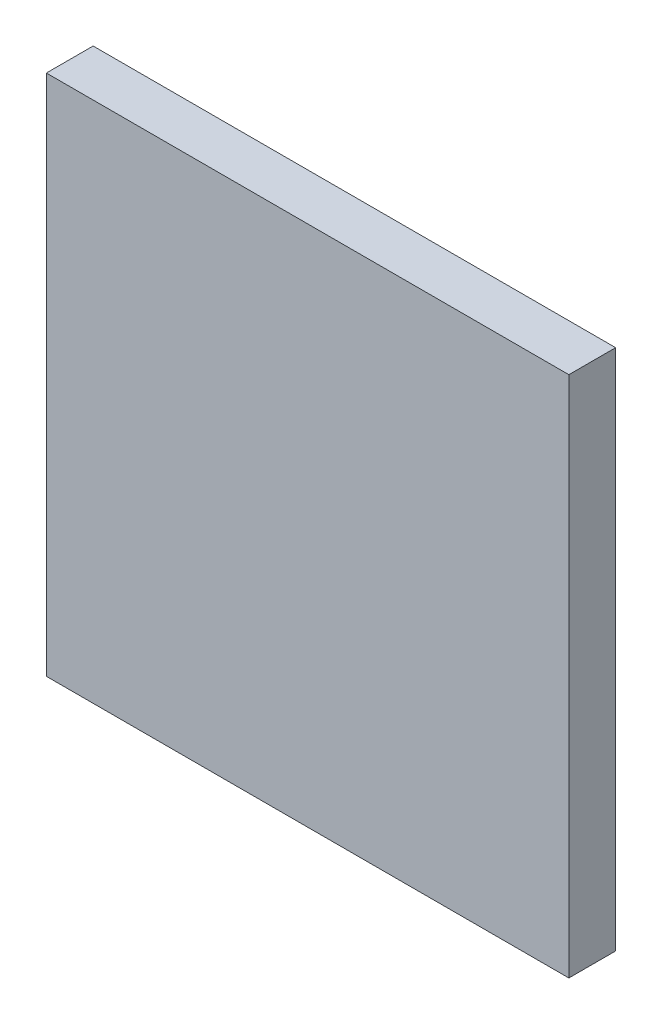
SolidWorks part; units mm, degrees
material "ABS PC"
ref_plane "Front Plane" through (0, 0, 0) normal (0, 0, 1) x (1, 0, 0)
ref_plane "Top Plane" through (0, 0, 0) normal (0, 1, 0) x (1, 0, 0)
ref_plane "Right Plane" through (0, 0, 0) normal (1, 0, 0) x (0, 0, -1)
sketch "Sketch1" plane through (0, 0, 0) normal (0, 0, 1) x (1, 0, 0)
  line L0 (-97.6376, 73.8886) -> (-97.6376, 56.1594)
  line L1 (-97.6376, 56.1594) -> (-79.9084, 56.1594)
  line L2 (-79.9084, 56.1594) -> (-79.9084, 73.8886)
  line L3 (-79.9084, 73.8886) -> (-97.6376, 73.8886)
  line L8 (-97.1296, 73.3806) -> (-97.1296, 56.6674) construction
  line L9 (-80.4164, 73.3806) -> (-97.1296, 73.3806) construction
  line L10 (-80.4164, 56.6674) -> (-80.4164, 73.3806) construction
  line L11 (-97.1296, 56.6674) -> (-80.4164, 56.6674) construction
  dimension "D1" = 16.7132
  dimension "D2" = 0.508
extrude "Boss-Extrude1" add sketch "Sketch1" along normal blind 1.5875
